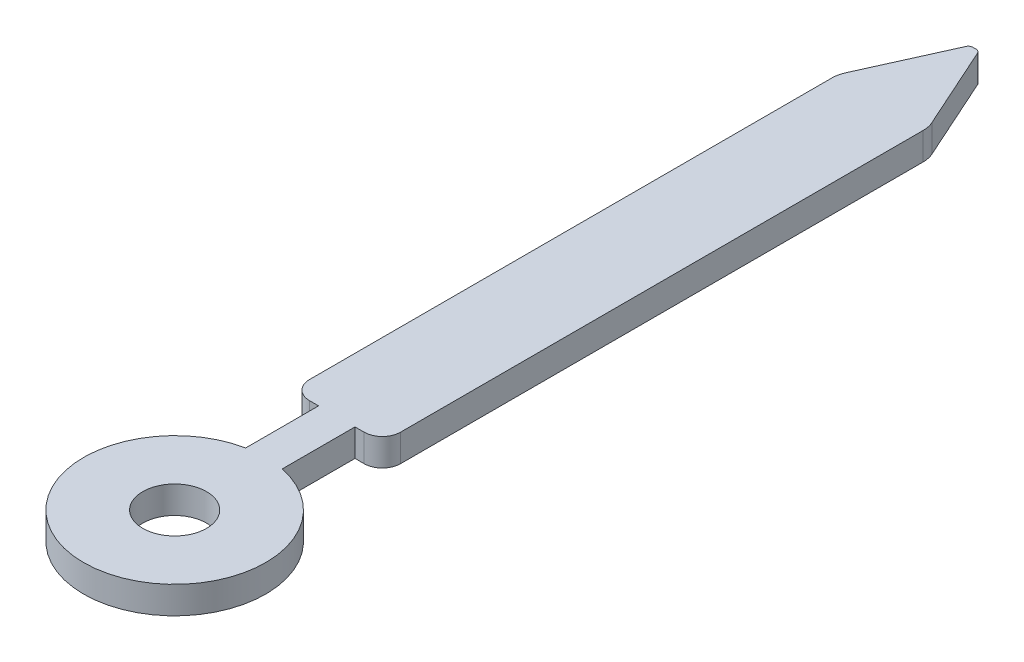
SolidWorks part; units mm, degrees
ref_plane "Front Plane" through (0, 0, 0) normal (0, 0, 1) x (1, 0, 0)
ref_plane "Top Plane" through (0, 0, 0) normal (0, 1, 0) x (1, 0, 0)
ref_plane "Right Plane" through (0, 0, 0) normal (1, 0, 0) x (0, 0, -1)
sketch "Sketch1" plane through (0, 0, 0) normal (0, 1, 0) x (1, 0, 0)
  line L0 (0.063, 6.9711) -> (0.4736, 6.0587)
  line L1 (-0.3, 0) -> (-0.2, 0)
  line L2 (-0.5, 0.2) -> (-0.5, 5.9356)
  line L3 (-0.0183, 7) -> (0.0183, 7)
  line L4 (0.5, 0.2) -> (0.5, 5.9356)
  line L5 (-0.063, 6.9711) -> (-0.4736, 6.0587)
  line L6 (0.2, 0) -> (0.2, -0.8)
  line L7 (-0.2, 0) -> (-0.2, -0.8)
  line L8 (0.2, 0) -> (0.3, 0)
  arc A0 (-0.063, 6.9711) -> (-0.0183, 7) centre (-0.0183, 6.951) cw
  arc A1 (0.063, 6.9711) -> (0.0183, 7) centre (0.0183, 6.951) ccw
  arc A2 (-0.4736, 6.0587) -> (-0.5, 5.9356) centre (-0.2, 5.9356) ccw
  arc A3 (0.4736, 6.0587) -> (0.5, 5.9356) centre (0.2, 5.9356) cw
  arc A4 (-0.2, -0.8) -> (0.2, -0.8) centre (0, -1.7798) ccw
  circle A5 centre (0, -1.7798) radius 0.35
  arc A6 (0.3, 0) -> (0.5, 0.2) centre (0.3, 0.2) ccw
  arc A7 (-0.3, 0) -> (-0.5, 0.2) centre (-0.3, 0.2) cw
  point P9 (-0.05, 7)
  point P12 (0.05, 7)
  point P15 (-0.5, 6)
  point P18 (0.5, 6)
  point P27 (0.5, 0)
  point P30 (-0.5, 0)
  dimension "D3" = 0.049
  dimension "D7" = 0.3
  dimension "D9" = 0.8
  dimension "D10" = 0.2
  dimension "D1" = 1
  dimension "D2" = 0.5
  dimension "D4" = 1
  dimension "D5" = 1
  dimension "D6" = 0.1
  dimension "D8" = 0.8
extrude "Boss-Extrude1" add sketch "Sketch1" along normal blind 0.3
